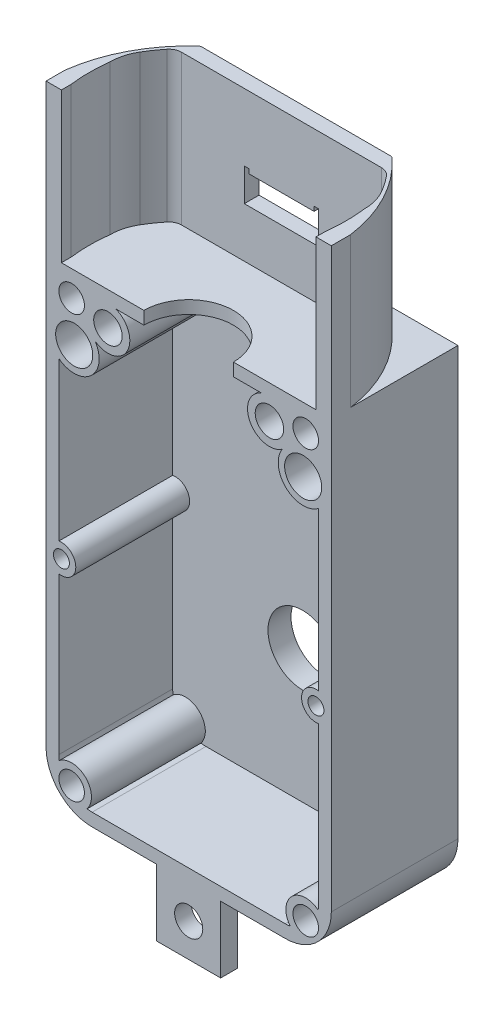
SolidWorks part; units mm, degrees
ref_plane "Front Plane" through (0, 0, 0) normal (0, 0, 1) x (1, 0, 0)
ref_plane "Top Plane" through (0, 0, 0) normal (0, 1, 0) x (1, 0, 0)
ref_plane "Right Plane" through (0, 0, 0) normal (1, 0, 0) x (0, 0, -1)
sketch "Sketch1" plane through (0, 0, 0) normal (0, 0, 1) x (1, 0, 0)
  line L0 (-9.95, -18.5) -> (-9.95, -1.55) construction
  line L1 (-7.55, -18.5) -> (7.55, -18.5)
  line L2 (-11.15, -14.9) -> (-11.15, 18.5)
  line L3 (-11.15, 18.5) -> (11.15, 18.5)
  line L4 (11.15, -14.9) -> (11.15, 18.5)
  line L5 (-11.15, -18.5) -> (11.15, 18.5) construction
  line L6 (-11.15, 18.5) -> (11.15, -18.5) construction
  line L7 (9.15, -18.5) -> (9.15, -16.5) construction
  line L8 (0, -18.5) -> (0, -7.2) construction
  line L9 (0, 0) -> (5.3483, 0)
  line L10 (8.95, 13.4566) -> (11.15, 13.4566)
  circle A0 centre (9.15, -16.5) radius 1
  circle A1 centre (-9.95, -1.55) radius 0.625
  circle A2 centre (9.95, -1.55) radius 0.625
  circle A3 centre (-9.15, -16.5) radius 1
  circle A4 centre (0, -7.2) radius 2.7
  circle A5 centre (9.15, 16.5) radius 1
  circle A6 centre (-9.15, 16.5) radius 1
  circle A7 centre (8.95, 13.4566) radius 1.45
  circle A8 centre (6.3127, 15.9) radius 1.1123
  circle A9 centre (-6.3127, 15.9) radius 1.1123
  circle A10 centre (-8.95, 13.4566) radius 1.45
  arc A11 (-11.15, -14.9) -> (-7.55, -18.5) centre (-7.55, -14.9) ccw
  arc A12 (11.15, -14.9) -> (7.55, -18.5) centre (7.55, -14.9) cw
  point P0 (0, 0)
  dimension "D7" = 2
  dimension "D8" = 1.25
  dimension "D10" = 5.4
  dimension "D12" = 2.9
  dimension "D13" = 2
  dimension "D17" = 3.6
  dimension "D1" = 22.3
  dimension "D2" = 37
  dimension "D3" = 16.95
  dimension "D4" = 1.2
  dimension "D5" = 2
  dimension "D6" = 2
  dimension "D9" = 11.3
  dimension "D11" = 2.2
  dimension "D14" = 3.05
  dimension "D15" = 2.6
  dimension "D16" = 2.9
extrude "Boss-Extrude1" add sketch "Sketch1" along normal blind 1
sketch "Sketch2" plane through (0, 0, 0) normal (0, 0, 1) x (1, 0, 0)
  line L0 (0, 18.5) -> (0, 11.4842) construction
  line L1 (-11.15, 18.5) -> (11.15, 18.5) construction
  line L2 (-11.15, -14.9) -> (-11.15, 18.5) construction
  line L3 (11.15, -14.9) -> (11.15, 18.5) construction
  line L4 (-7.55, -18.5) -> (7.55, -18.5) construction
  line L5 (-11.15, -14.9) -> (-11.15, 18.5)
  line L6 (-11.15, 18.5) -> (11.15, 18.5)
  line L7 (11.15, -14.9) -> (11.15, 18.5)
  line L8 (-7.55, -18.5) -> (7.55, -18.5)
  line L9 (-10.15, -14.9) -> (-10.15, -2.6571)
  line L10 (-10.15, -0.4429) -> (-10.15, 11.9195)
  line L11 (10.15, -14.9) -> (10.15, -2.6571)
  line L12 (-7.55, -17.5) -> (7.55, -17.5)
  line L13 (10.15, -14.9) -> (10.15, 17.5) construction
  line L14 (-10.15, -14.9) -> (-10.15, 17.5) construction
  line L15 (-5.7028, 17.5) -> (5.7028, 17.5)
  line L16 (-10.15, 17.5) -> (10.15, 17.5) construction
  line L17 (10.15, -0.4429) -> (10.15, 11.9195)
  arc A0 (-7.9413, -17.4704) -> (-10.1204, -15.2913) centre (-9.15, -16.5) ccw
  circle A1 centre (-6.3127, 15.9) radius 1.1123 construction
  circle A2 centre (-6.3127, 15.9) radius 1.7123
  arc A3 (-7.3059, 14.5051) -> (-5.7028, 17.5) centre (-6.3127, 15.9) ccw
  circle A4 centre (-6.3127, 15.9) radius 1.1123
  circle A5 centre (-8.95, 13.4566) radius 1.45 construction
  circle A6 centre (-8.95, 13.4566) radius 1.45
  arc A7 (-10.15, 11.9195) -> (-7.3059, 14.5051) centre (-8.95, 13.4566) ccw
  circle A8 centre (-9.95, -1.55) radius 0.625 construction
  circle A9 centre (-9.95, -1.55) radius 0.625
  arc A10 (-10.15, -2.6571) -> (-10.15, -0.4429) centre (-9.95, -1.55) ccw
  circle A11 centre (-9.15, -16.5) radius 1 construction
  circle A12 centre (-9.15, -16.5) radius 1
  circle A13 centre (9.15, -16.5) radius 1
  circle A15 centre (9.95, -1.55) radius 0.625
  arc A16 (10.15, -2.6571) -> (10.15, -0.4429) centre (9.95, -1.55) cw
  circle A17 centre (8.95, 13.4566) radius 1.45
  arc A18 (10.15, 11.9195) -> (7.3059, 14.5051) centre (8.95, 13.4566) cw
  circle A19 centre (6.3127, 15.9) radius 1.1123
  arc A20 (7.3059, 14.5051) -> (5.7028, 17.5) centre (6.3127, 15.9) cw
  arc A21 (7.55, -18.5) -> (11.15, -14.9) centre (7.55, -14.9) ccw construction
  arc A22 (-11.15, -14.9) -> (-7.55, -18.5) centre (-7.55, -14.9) ccw construction
  arc A23 (7.55, -18.5) -> (11.15, -14.9) centre (7.55, -14.9) ccw
  arc A24 (-11.15, -14.9) -> (-7.55, -18.5) centre (-7.55, -14.9) ccw
  arc A25 (7.55, -17.5) -> (7.9413, -17.4704) centre (7.55, -14.9) ccw
  arc A26 (-10.15, -14.9) -> (-10.1204, -15.2913) centre (-7.55, -14.9) ccw
  circle A27 centre (-8.95, 13.4566) radius 1.95 construction
  circle A28 centre (-9.15, 16.5) radius 1 construction
  circle A29 centre (-9.15, 16.5) radius 1
  circle A30 centre (9.15, 16.5) radius 1 construction
  circle A31 centre (9.15, 16.5) radius 1
  circle A32 centre (-9.95, -1.55) radius 1.125 construction
  circle A33 centre (-9.15, -16.5) radius 1.55 construction
  arc A34 (-7.9413, -17.4704) -> (-7.55, -17.5) centre (-7.55, -14.9) ccw
  arc A35 (-10.15, -14.9) -> (-7.55, -17.5) centre (-7.55, -14.9) ccw construction
  arc A36 (10.1204, -15.2913) -> (10.15, -14.9) centre (7.55, -14.9) ccw
  arc A37 (7.55, -17.5) -> (10.15, -14.9) centre (7.55, -14.9) ccw construction
  arc A38 (7.9413, -17.4704) -> (10.1204, -15.2913) centre (9.15, -16.5) cw
  dimension "D1" = 0.6
  dimension "D2" = 0.5
  dimension "D3" = 0.5
  dimension "D4" = 0.55
  dimension "D5" = 1
extrude "Boss-Extrude2" add sketch "Sketch2" along normal blind 9.9
sketch "Sketch3" plane through (0, 0, 1) normal (0, 0, 1) x (1, 0, 0)
  line L0 (5.7028, 17.5) -> (-5.7028, 17.5) construction
  line L1 (5.7028, 17.5) -> (4.3272, 17.5)
  line L2 (-4.3272, 17.5) -> (-5.7028, 17.5)
  arc A0 (-7, 13.4444) -> (-4.3272, 17.5) centre (-6.3127, 15.9) ccw
  arc A1 (4.3272, 17.5) -> (7, 13.4444) centre (6.3127, 15.9) ccw
  arc A2 (-7.3059, 14.5051) -> (-5.7028, 17.5) centre (-6.3127, 15.9) ccw construction
  arc A3 (-7.3059, 14.5051) -> (-5.7028, 17.5) centre (-6.3127, 15.9) ccw
  arc A4 (-10.15, 11.9195) -> (-7.3059, 14.5051) centre (-8.95, 13.4566) ccw construction
  arc A5 (-7, 13.4444) -> (-7.3059, 14.5051) centre (-8.95, 13.4566) ccw
  arc A6 (5.7028, 17.5) -> (7.3059, 14.5051) centre (6.3127, 15.9) ccw construction
  arc A7 (5.7028, 17.5) -> (7.3059, 14.5051) centre (6.3127, 15.9) ccw
  arc A8 (7.3059, 14.5051) -> (10.15, 11.9195) centre (8.95, 13.4566) ccw construction
  arc A9 (7.3059, 14.5051) -> (7, 13.4444) centre (8.95, 13.4566) ccw
  dimension "D1" = 5.1
  dimension "D2" = 5.1
extrude "Boss-Extrude3" add sketch "Sketch3" along normal blind 1.55
sketch "Sketch4" plane through (0, 0, 0) normal (0, 0, -1) x (-1, 0, 0)
  line L0 (0, 18.5) -> (0, 14.3921) construction
  line L1 (11.15, 18.5) -> (-11.15, 18.5) construction
  circle A0 centre (-6.3127, 15.9) radius 2.2
  circle A1 centre (6.3127, 15.9) radius 2.2
  dimension "D1" = 4.4
extrude "Cut-Extrude1" cut sketch "Sketch4" against normal blind 2.1
sketch "Sketch5" plane through (0, 0, 0) normal (0, 0, -1) x (-1, 0, 0)
  circle A0 centre (0, -7.2) radius 3.55
  circle A1 centre (0, -7.2) radius 2.7 construction
  circle A2 centre (0, -7.2) radius 2.7
  dimension "D1" = 7.1
extrude "Boss-Extrude4" add sketch "Sketch5" along normal blind 0.8
sketch "Sketch6" plane through (0, 0, 0) normal (0, 0, -1) x (-1, 0, 0)
  circle A0 centre (0, 4.45) radius 2.05
extrude "Boss-Extrude5" add sketch "Sketch6" along normal blind 2.4
sketch "Sketch7" plane through (0, 0, 9.9) normal (0, 0, 1) x (1, 0, 0)
  line L0 (-7.55, -18.5) -> (7.55, -18.5) construction
  line L1 (-2.5, -18.5) -> (2.5, -18.5)
  line L3 (-2.5, -18.5) -> (-2.5, -23.7)
  line L4 (-2.5, -23.7) -> (2.5, -23.7)
  line L5 (2.5, -18.5) -> (2.5, -23.7)
  circle A0 centre (0, -21.1) radius 1.1
  point P0 (0, -18.5)
  point P1 (0, -18.5)
  dimension "D2" = 2.2
  dimension "D1" = 5
extrude "Boss-Extrude6" add sketch "Sketch7" against normal blind 1.3
sketch "Sketch8" plane through (0, 18.5, 0) normal (0, 1, 0) x (1, 0, 0)
  line L0 (11.15, -9.9) -> (-11.15, -9.9) construction
  line L1 (3.5, -9.9) -> (-3.5, -9.9)
  arc A0 (3.5, -9.9) -> (-3.5, -9.9) centre (0, -9.9) ccw
  dimension "D1" = 7
extrude "Cut-Extrude2" cut sketch "Sketch8" against normal blind 1.3
sketch "Sketch9" plane through (0, 18.5, 0) normal (0, 1, 0) x (1, 0, 0)
  line L0 (-2.5, -9.9) -> (2.5, -9.9) construction
  line L1 (-9.95, -9.9) -> (-9.95, -9.1592)
  line L2 (9.95, -9.9) -> (9.95, -9.1592)
  line L3 (11.15, -9.9) -> (3.5, -9.9) construction
  line L4 (7.4835, -1.5) -> (-7.4835, -1.5)
  line L5 (0, -9.9) -> (0, -4.9263) construction
  line L6 (11.15, -9.9) -> (9.95, -9.9)
  line L7 (-9.95, -9.9) -> (-11.15, -9.9)
  line L8 (7.8062, -2.65) -> (-7.8062, -2.65)
  line L9 (11.15, -9.9) -> (11.15, 0) construction
  line L10 (11.15, -9.9) -> (11.15, -8.4033)
  line L11 (-11.15, -9.9) -> (-11.15, 0) construction
  line L12 (-11.15, -9.9) -> (-11.15, -8.4033)
  arc A0 (11.15, -8.4033) -> (7.4835, -1.5) centre (0, -9.9) ccw
  arc A1 (9.4392, -4.2518) -> (8.5869, -3.025) centre (0, -9.9) ccw
  arc A2 (-7.4835, -1.5) -> (-11.15, -8.4033) centre (0, -9.9) ccw
  arc A3 (-8.5869, -3.025) -> (-9.4392, -4.2518) centre (0, -9.9) ccw
  arc A4 (-9.95, -6.1003) -> (-9.4392, -4.2518) centre (-6.35, -6.1003) cw
  arc A5 (9.95, -6.1003) -> (9.4392, -4.2518) centre (6.35, -6.1003) ccw
  arc A6 (-7.8062, -2.65) -> (-8.5869, -3.025) centre (-7.8062, -3.65) ccw
  arc A7 (7.8062, -2.65) -> (8.5869, -3.025) centre (7.8062, -3.65) cw
  arc A8 (9.95, -9.1592) -> (9.95, -6.1003) centre (-2.0177, -7.6298) ccw
  arc A9 (-9.95, -9.1592) -> (-9.95, -6.1003) centre (2.0177, -7.6298) cw
  point P2 (0, -9.9)
  point P28 (-8.2727, -2.65)
  dimension "D3" = 1.2
  dimension "D2" = 22
  dimension "D4" = 3.6
  dimension "D5" = 1
  dimension "D6" = 24.13
  dimension "D1" = 0
extrude "Boss-Extrude7" add sketch "Sketch9" along normal blind 11.7
sketch "Sketch10" plane through (0, 0, 2.65) normal (0, 0, 1) x (1, 0, 0)
  line L2 (0, 24.6) -> (0, 22.4) construction
  line L3 (2.55, 24.6) -> (-2.55, 24.6)
  line L4 (2.9, 24.6) -> (2.9, 22.4)
  line L5 (2.9, 22.4) -> (-2.9, 22.4)
  line L6 (-2.9, 24.6) -> (-2.9, 22.4)
  line L7 (2.9, 24.6) -> (-2.9, 22.4) construction
  line L8 (2.9, 22.4) -> (-2.9, 24.6) construction
  line L10 (2.55, 24.6) -> (2.55, 24.95)
  line L12 (-2.55, 24.6) -> (-2.55, 24.95)
  line L13 (2.55, 24.0735) -> (0, 24.6) construction
  line L15 (-2.9, 24.95) -> (-2.55, 24.95)
  line L17 (-2.9, 24.95) -> (-2.9, 24.6)
  line L18 (2.9, 24.95) -> (2.9, 24.6)
  line L19 (2.55, 24.95) -> (2.9, 24.95)
  line L20 (0, 24.6) -> (-2.55, 24.0735) construction
  point P0 (0, 23.5)
extrude "Cut-Extrude3" cut sketch "Sketch10" against normal blind 1.7
sketch "Sketch11" plane through (0, 0, 1.5) normal (0, 0, -1) x (-1, 0, 0)
  line L1 (2.55, 24.6) -> (-2.55, 24.6)
  line L2 (2.55, 24.6) -> (2.55, 26.2)
  line L3 (2.55, 26.2) -> (-2.55, 26.2)
  line L4 (-2.55, 24.6) -> (-2.55, 26.2)
  dimension "D1" = 1.6
extrude "Boss-Extrude8" add sketch "Sketch11" along normal blind 3
sketch "Sketch12" plane through (0, 26.2, 0) normal (0, 1, 0) x (1, 0, 0)
  line L0 (-2.55, 1.5) -> (-2.55, -1.5) construction
  line L1 (2.55, 1.5) -> (-2.55, 1.5)
  line L2 (2.55, 1.5) -> (2.55, 0.5)
  line L3 (2.55, 0.5) -> (-2.55, 0.5)
  line L4 (-2.55, 1.5) -> (-2.55, 0.5)
  dimension "D1" = 1
extrude "Boss-Extrude9" add sketch "Sketch12" against normal blind 2.5
sketch "Sketch13" plane through (0, 0, 1) normal (0, 0, 1) x (1, 0, 0)
  circle A2 centre (0, 4.45) radius 1
  dimension "D1" = 2
extrude "Cut-Extrude4" cut sketch "Sketch13" against normal blind 2.5
fillet "Fillet1" radius 0.3 1 edges at (-2.05, 4.45, -2.4)
fillet "Fillet2" radius 0.3 2 edges at (7.4835, 24.35, 1.5) (-7.4835, 24.35, 1.5)
